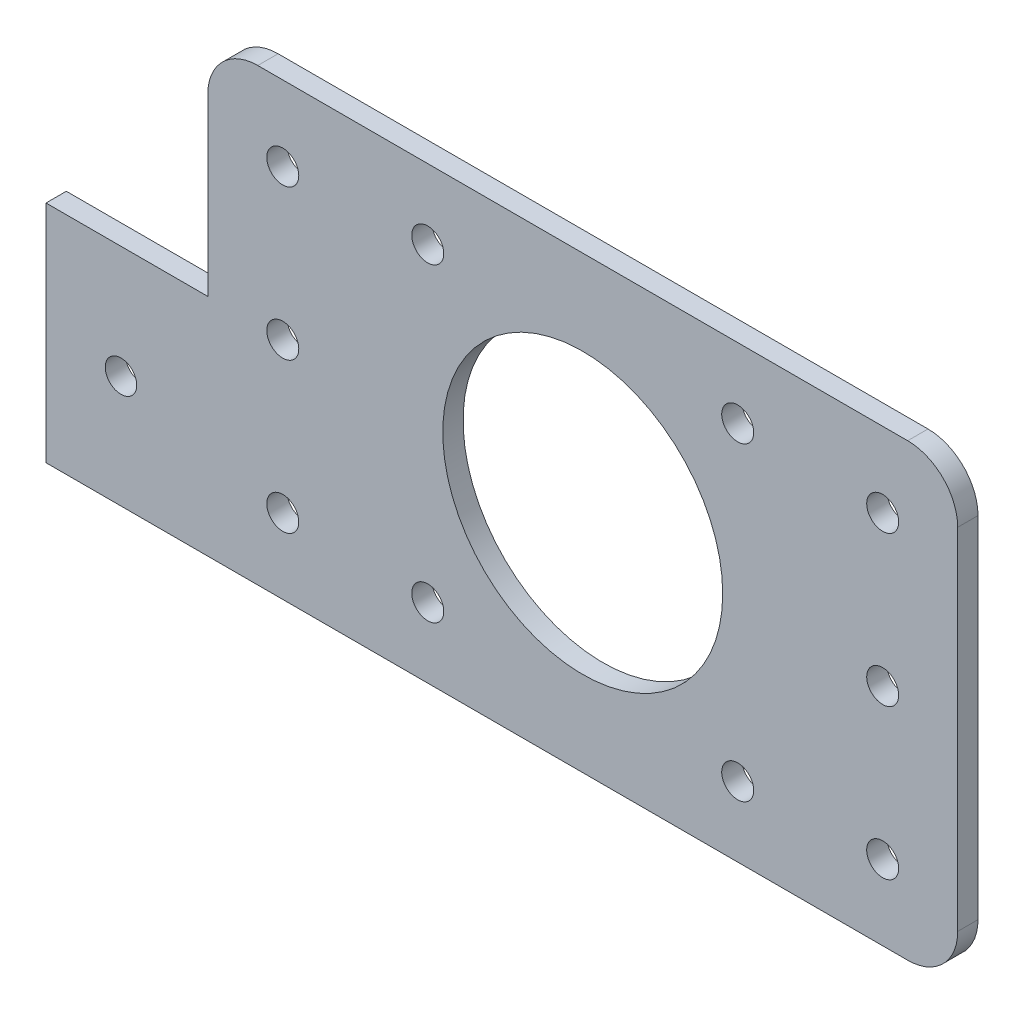
SolidWorks part; units mm, degrees
ref_plane "Front Plane" through (0, 0, 0) normal (0, 0, 1) x (1, 0, 0)
ref_plane "Top Plane" through (0, 0, 0) normal (0, 1, 0) x (1, 0, 0)
ref_plane "Right Plane" through (0, 0, 0) normal (1, 0, 0) x (0, 0, -1)
sketch "Sketch1" plane through (0, 0, 0) normal (0, 0, 1) x (1, 0, 0)
  line L0 (22.5, 22.5) -> (22.5, -22.5) construction
  line L1 (-37.5, -22.5) -> (37.5, -22.5)
  line L2 (-37.5, -22.5) -> (-37.5, 22.5)
  line L3 (-37.5, 22.5) -> (37.5, 22.5)
  line L4 (37.5, -22.5) -> (37.5, 22.5)
  line L5 (-37.5, -22.5) -> (37.5, 22.5) construction
  line L6 (-37.5, 22.5) -> (37.5, -22.5) construction
  line L7 (-15.5, -15.5) -> (15.5, -15.5) construction
  line L8 (-15.5, -15.5) -> (-15.5, 15.5) construction
  line L9 (-15.5, 15.5) -> (15.5, 15.5) construction
  line L10 (15.5, -15.5) -> (15.5, 15.5) construction
  line L11 (-15.5, -15.5) -> (15.5, 15.5) construction
  line L12 (-15.5, 15.5) -> (15.5, -15.5) construction
  line L13 (-22.5, 22.5) -> (-22.5, -22.5) construction
  circle A0 centre (0, 0) radius 14
  circle A1 centre (-15.5, 15.5) radius 1.6
  circle A2 centre (15.5, 15.5) radius 1.6
  circle A3 centre (15.5, -15.5) radius 1.6
  circle A4 centre (-15.5, -15.5) radius 1.6
  point P0 (0, 0)
  dimension "D2" = 28
  dimension "D3" = 3.2
  dimension "D1" = 31
  dimension "D4" = 45
  dimension "D5" = 75
  dimension "D6" = 15
  dimension "D7" = 15
extrude "Boss-Extrude1" add sketch "Sketch1" along normal blind 2.032
fillet "Fillet2" radius 5 4 edges at (37.5, 22.5, 1.016) (37.5, -22.5, 1.016) (-37.5, -22.5, 1.016) (-37.5, 22.5, 1.016)
sketch "Sketch2" plane through (0, 0, 2.032) normal (0, 0, 1) x (1, 0, 0)
  line L0 (0, 40.4519) -> (0, -37.5654) construction
  line L1 (0, -54.6431) -> (0, 54.6431) construction
  line L2 (47.3483, 0) -> (-47.3483, 0) construction
  line L3 (55, 0) -> (-55, 0) construction
  line L4 (-37.5, 17.5) -> (-37.5, -17.5) construction
  circle A0 centre (-30, 0) radius 1.6
  circle A1 centre (-30, 15) radius 1.6
  circle A2 centre (-30, -15) radius 1.6
  circle A3 centre (30, -15) radius 1.6
  circle A4 centre (30, 15) radius 1.6
  circle A5 centre (30, 0) radius 1.6
  dimension "D1" = 3.2
  dimension "D2" = 7.5
  dimension "D3" = 15
extrude "Cut-Extrude1" cut sketch "Sketch2" against normal through all
sketch "Alignment Sketch 1" plane through (0, 0, 2.032) normal (0, 0, 1) x (1, 0, 0)
  line L0 (-30, 15) -> (-30, -15) construction
  line L1 (30, 15) -> (30, -15) construction
  circle A0 centre (30, 15) radius 1.6 construction
  point P0 (-30, 15)
  point P1 (-30, 0)
  point P3 (-30, -15)
  point P5 (30, 15)
  point P7 (30, 0)
  point P8 (30, -15)
sketch "Sketch4" plane through (0, 0, 0) normal (0, 0, -1) x (-1, 0, 0)
  line L1 (53.68, 0) -> (32.5, 0)
  line L2 (53.68, 0) -> (53.68, -22.5)
  line L3 (53.68, -22.5) -> (32.5, -22.5)
  line L4 (32.5, 0) -> (32.5, -22.5)
  line L5 (53.68, 0) -> (32.5, -22.5) construction
  line L6 (53.68, -22.5) -> (32.5, 0) construction
  line L8 (32.5, -22.5) -> (-32.5, -22.5) construction
  line L9 (37.5, 17.5) -> (37.5, -17.5) construction
  point P0 (43.09, -11.25)
  dimension "D1" = 16.18
extrude "Boss-Extrude2" add sketch "Sketch4" against normal up to surface (2.032 mm away) up to face at (28.4, 0, 2.032)
sketch "Mounting Hole Sketch" plane through (0, 0, 2.032) normal (0, 0, 1) x (1, 0, 0)
  line L0 (-53.68, 0) -> (-53.68, -22.5) construction
  line L1 (-46.18, 0) -> (-46.18, -22.5) construction
  line L2 (-37.5, 0) -> (-53.68, 0) construction
  line L3 (-53.68, -22.5) -> (32.5, -22.5) construction
  circle A0 centre (-46.18, -11.25) radius 1.575
  point P10 (-46.18, -11.25)
  dimension "D2" = 3.15
  dimension "D3" = 7.5
extrude "Mounting Hole Cut" cut sketch "Mounting Hole Sketch" against normal through all
